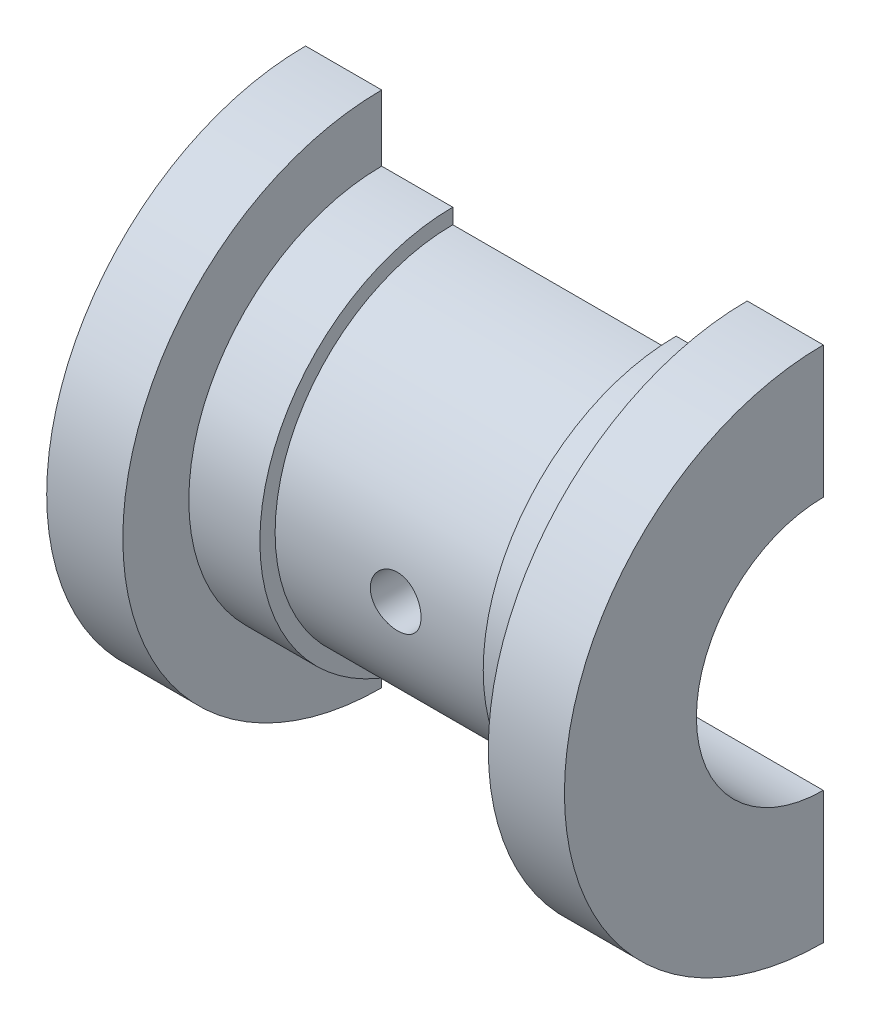
SolidWorks part; units mm, degrees
ref_plane "Front Plane" through (0, 0, 0) normal (0, 0, 1) x (1, 0, 0)
ref_plane "Top Plane" through (0, 0, 0) normal (0, 1, 0) x (1, 0, 0)
ref_plane "Right Plane" through (0, 0, 0) normal (1, 0, 0) x (0, 0, -1)
sketch "Sketch1" plane through (0, 0, 0) normal (0, 0, 1) x (1, 0, 0)
  line L0 (-76.9811, 0) -> (125.4792, 0) construction
  line L1 (0, 0) -> (0, 25.5)
  line L2 (0, 25.5) -> (7.5, 25.5)
  line L3 (7.5, 25.5) -> (7.5, 19)
  line L4 (7.5, 19) -> (14.5, 19)
  line L5 (14.5, 19) -> (14.5, 17.5)
  line L6 (14.5, 17.5) -> (36.5, 17.5)
  line L7 (36.5, 17.5) -> (36.5, 19)
  line L8 (36.5, 19) -> (43.5, 19)
  line L9 (43.5, 19) -> (43.5, 25.5)
  line L10 (43.5, 25.5) -> (51, 25.5)
  line L11 (51, 25.5) -> (51, 0)
  line L12 (0, 0) -> (51, 0)
  dimension "D1" = 51
  dimension "D2" = 36
  dimension "D3" = 22
  dimension "D4" = 51
  dimension "D5" = 38
  dimension "D6" = 35
revolve "Revolve1" add sketch "Sketch1" angle 180 about L12
sketch "Sketch2" plane through (0, 0, 0) normal (-1, 0, 0) x (0, 0, 1)
  line L0 (0, -25.5) -> (0, 25.5) construction
  line L1 (0, -12.5) -> (0, 12.5)
  arc A0 (0, -12.5) -> (0, 12.5) centre (0, 0) ccw
  dimension "D1" = 25
extrude "Cut-Extrude1" cut sketch "Sketch2" against normal through all
hole_wizard "Ø5.0mm Dowel Hole1" positions "3DSketch1" profile "Sketch3" hole size "Ø5.0" standard "ANSI Metric"
sketch3d "3DSketch1"
  line L0 (0, 0, 0) -> (51, 0, 0) construction
  line L1 (51, 0, 0) -> (0, 0, 0) construction
  line L3 (26.4927, 0, 0) -> (26.4927, -10.8326, 0) construction
  point P0 (26.3759, -0.0292, 12.5)
sketch "Sketch3" plane through (26.3759, -0.0292, 12.5) normal (1, 0, 0) x (0, 1, 0.0023)
  line L0 (0, 0) -> (0, 22.6922)
  line L1 (0, 22.6922) -> (2.5, 21.19)
  line L2 (2.5, 21.19) -> (2.5, 0)
  line L5 (2.5, 0) -> (0, 0)
  line L10 (0, 22.6922) -> (-2.5, 21.19) construction
  line L11 (0, -6.35) -> (0, 107.95) construction
  dimension "Hole Dia." = 5
  dimension "Hole Depth" = 21.19
  dimension "Drill Angle" = 118
